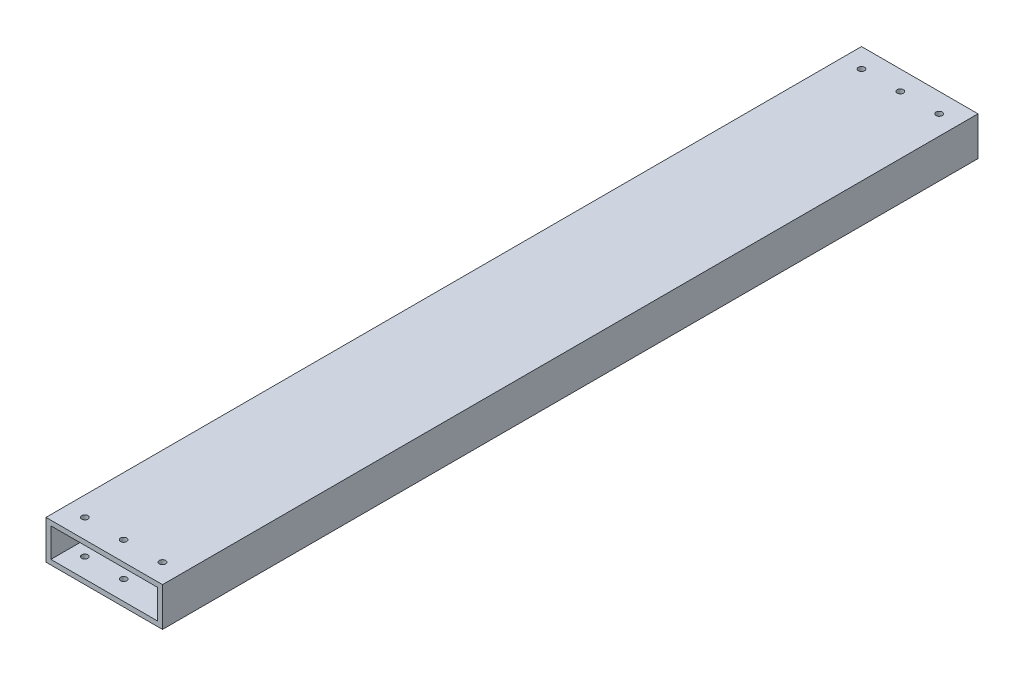
SolidWorks part; units mm, degrees
ref_plane "Front" through (0, 0, 0) normal (0, 0, 1) x (1, 0, 0)
ref_plane "Top" through (0, 0, 0) normal (0, 1, 0) x (1, 0, 0)
ref_plane "Right" through (0, 0, 0) normal (1, 0, 0) x (0, 0, -1)
sketch "Sketch1" plane through (0, 0, 0) normal (0, 0, 1) x (1, 0, 0)
  line L1 (-38.1, -12.7) -> (38.1, -12.7)
  line L2 (-38.1, -12.7) -> (-38.1, 12.7)
  line L3 (-38.1, 12.7) -> (38.1, 12.7)
  line L4 (38.1, -12.7) -> (38.1, 12.7)
  line L5 (-38.1, -12.7) -> (38.1, 12.7) construction
  line L6 (-38.1, 12.7) -> (38.1, -12.7) construction
  point P0 (0, 0)
  dimension "D1" = 25.4
  dimension "D2" = 76.2
extrude "Extrude-Thin1" add sketch "Sketch1" along normal mid plane 533.4 thin thin type one direction reverse wall 3.175
sketch "Sketch2" plane through (0, 12.7, 0) normal (0, 1, 0) x (1, 0, 0)
  line L0 (38.1, 254) -> (-38.1, 254) construction
  line L1 (38.1, -266.7) -> (38.1, 266.7) construction
  line L2 (-38.1, -266.7) -> (-38.1, 266.7) construction
  line L3 (-38.1, -254) -> (38.1, -254) construction
  line L4 (38.1, 266.7) -> (-38.1, 266.7) construction
  line L5 (38.1, -266.7) -> (-38.1, -266.7) construction
  circle A0 centre (25.4, 254) radius 2.032
  circle A1 centre (0, 254) radius 2.032
  circle A2 centre (25.4, -254) radius 2.032
  circle A3 centre (0, -254) radius 2.032
  circle A4 centre (-25.4, 254) radius 2.032
  circle A5 centre (-25.4, -254) radius 2.032
  point P24 (0, 0)
  dimension "D3" = 4.064
  dimension "D1" = 12.7
  dimension "D2" = 12.7
  dimension "D4" = 12.7
  dimension "D5" = 25.4
  dimension "D6" = 25.4
extrude "Cut-Extrude1" cut sketch "Sketch2" against normal through all contours A0 | A1 | A2 | A3 | A4 | A5
equation "\"D2@Sketch2\"=\"D1@Sketch2\""
